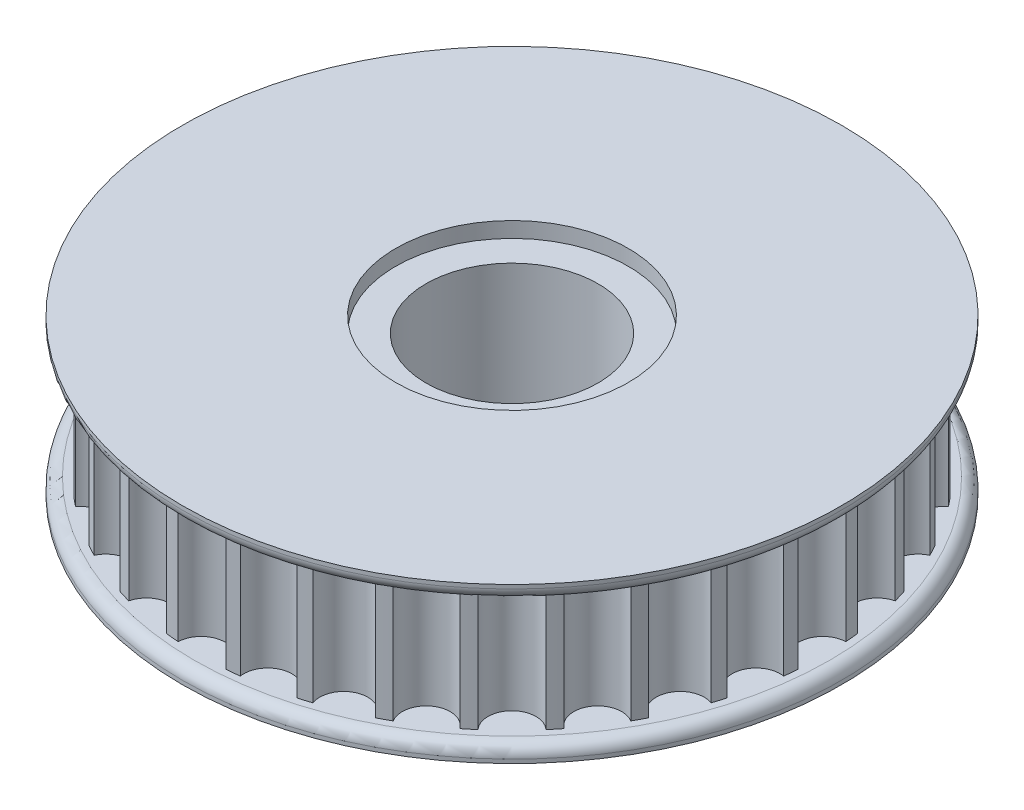
SolidWorks part; units mm, degrees
ref_plane "Front Plane" through (0, 0, 0) normal (0, 0, 1) x (1, 0, 0)
ref_plane "Top Plane" through (0, 0, 0) normal (0, 1, 0) x (1, 0, 0)
ref_plane "Right Plane" through (0, 0, 0) normal (1, 0, 0) x (0, 0, -1)
sketch "Sketch1" plane through (0, 0, 0) normal (0, 1, 0) x (1, 0, 0)
  line L0 (0, -55) -> (0, 55) construction
  circle A0 centre (0, 0) radius 40.08
  arc A1 (-3.0977, 39.9601) -> (3.0977, 39.9601) centre (0, 40.08) ccw
  arc A2 (4.7577, 39.7966) -> (10.834, 38.588) centre (7.8192, 39.3099) ccw
  arc A3 (12.4302, 38.1038) -> (18.154, 35.7329) centre (15.338, 37.0291) ccw
  arc A4 (19.625, 34.9466) -> (24.7763, 31.5046) centre (22.2673, 33.3253) ccw
  arc A5 (26.0657, 30.4465) -> (30.4465, 26.0657) centre (28.3408, 28.3408) ccw
  arc A6 (31.5046, 24.7763) -> (34.9466, 19.625) centre (33.3253, 22.2673) ccw
  arc A7 (35.7329, 18.154) -> (38.1038, 12.4302) centre (37.0291, 15.338) ccw
  arc A8 (38.588, 10.834) -> (39.7966, 4.7577) centre (39.3099, 7.8192) ccw
  arc A9 (39.9601, 3.0977) -> (39.9601, -3.0977) centre (40.08, 0) ccw
  arc A10 (39.7966, -4.7577) -> (38.588, -10.834) centre (39.3099, -7.8192) ccw
  arc A11 (38.1038, -12.4302) -> (35.7329, -18.154) centre (37.0291, -15.338) ccw
  arc A12 (34.9466, -19.625) -> (31.5046, -24.7763) centre (33.3253, -22.2673) ccw
  arc A13 (30.4465, -26.0657) -> (26.0657, -30.4465) centre (28.3408, -28.3408) ccw
  arc A14 (24.7763, -31.5046) -> (19.625, -34.9466) centre (22.2673, -33.3253) ccw
  arc A15 (18.154, -35.7329) -> (12.4302, -38.1038) centre (15.338, -37.0291) ccw
  arc A16 (10.834, -38.588) -> (4.7577, -39.7966) centre (7.8192, -39.3099) ccw
  arc A17 (3.0977, -39.9601) -> (-3.0977, -39.9601) centre (0, -40.08) ccw
  arc A18 (-4.7577, -39.7966) -> (-10.834, -38.588) centre (-7.8192, -39.3099) ccw
  arc A19 (-12.4302, -38.1038) -> (-18.154, -35.7329) centre (-15.338, -37.0291) ccw
  arc A20 (-19.625, -34.9466) -> (-24.7763, -31.5046) centre (-22.2673, -33.3253) ccw
  arc A21 (-26.0657, -30.4465) -> (-30.4465, -26.0657) centre (-28.3408, -28.3408) ccw
  arc A22 (-31.5046, -24.7763) -> (-34.9466, -19.625) centre (-33.3253, -22.2673) ccw
  arc A23 (-35.7329, -18.154) -> (-38.1038, -12.4302) centre (-37.0291, -15.338) ccw
  arc A24 (-38.588, -10.834) -> (-39.7966, -4.7577) centre (-39.3099, -7.8192) ccw
  arc A25 (-39.9601, -3.0977) -> (-39.9601, 3.0977) centre (-40.08, 0) ccw
  arc A26 (-39.7966, 4.7577) -> (-38.588, 10.834) centre (-39.3099, 7.8192) ccw
  arc A27 (-38.1038, 12.4302) -> (-35.7329, 18.154) centre (-37.0291, 15.338) ccw
  arc A28 (-34.9466, 19.625) -> (-31.5046, 24.7763) centre (-33.3253, 22.2673) ccw
  arc A29 (-30.4465, 26.0657) -> (-26.0657, 30.4465) centre (-28.3408, 28.3408) ccw
  arc A30 (-24.7763, 31.5046) -> (-19.625, 34.9466) centre (-22.2673, 33.3253) ccw
  arc A31 (-18.154, 35.7329) -> (-12.4302, 38.1038) centre (-15.338, 37.0291) ccw
  arc A32 (-10.834, 38.588) -> (-4.7577, 39.7966) centre (-7.8192, 39.3099) ccw
  circle A33 centre (0, 0) radius 11.1
  point P10 (0, 36.98)
  point P99 (0, 0)
  dimension "D1" = 3.1
  dimension "D2" = 32
  dimension "D4" = 22.2
  dimension "D3" = 80.16
extrude "Boss-Extrude1" add sketch "Sketch1" along normal mid plane 16 contours A32 A0 A31 A30 A29 A28 A27 A26 A25 A24 A23 A22 A21 A20 A19 A18 A17 A16 A15 A14 A13 A12 A11 A10 A9 A8 A7
sketch "Sketch2" plane through (0, 8, 0) normal (0, 1, 0) x (1, 0, 0)
  circle A0 centre (0, 0) radius 15
  circle A1 centre (0, 0) radius 42.5
  dimension "D1" = 30
  dimension "D2" = 85
extrude "Boss-Extrude2" add sketch "Sketch2" along normal blind 2
mirror "Mirror1" about plane through (0, 0, 0) normal (0, 1, 0) of "Boss-Extrude2"
fillet "Fillet1" radius 1.5 2 edges at (0, 8, 42.5) (0, -8, 42.5)
